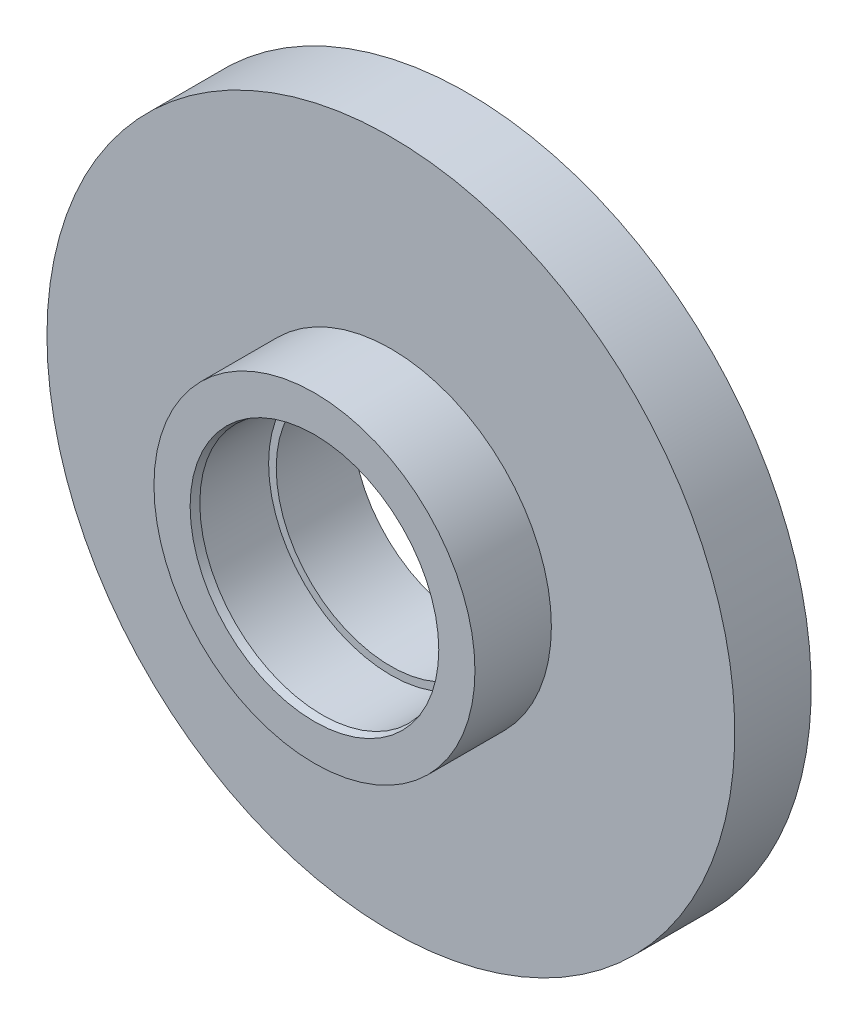
SolidWorks part; units mm, degrees
ref_plane "Front Plane" through (0, 0, 0) normal (0, 0, 1) x (1, 0, 0)
ref_plane "Top Plane" through (0, 0, 0) normal (0, 1, 0) x (1, 0, 0)
ref_plane "Right Plane" through (0, 0, 0) normal (1, 0, 0) x (0, 0, -1)
sketch "Sketch1" plane through (0, 0, 0) normal (0, 1, 0) x (1, 0, 0)
  line L0 (16, 0) -> (16, 10)
  line L1 (16, 10) -> (15, 10)
  line L2 (16, 0) -> (21, 0)
  line L3 (21, 0) -> (21, 10)
  line L4 (21, 10) -> (45, 10)
  line L5 (45, 10) -> (45, 20)
  line L6 (45, 20) -> (15, 20)
  line L7 (15, 20) -> (15, 10)
  line L8 (0, 0) -> (0, -29.3067) construction
  dimension "D1" = 16
  dimension "D2" = 5
  dimension "D3" = 10
  dimension "D4" = 10
  dimension "D5" = 10
  dimension "D6" = 45
  dimension "D7" = 15
revolve "Revolve1" add sketch "Sketch1" angle 360 about L8
chamfer "Chamfer1" distance 1 angle 15 1 edges at (-16, 0, 0)
